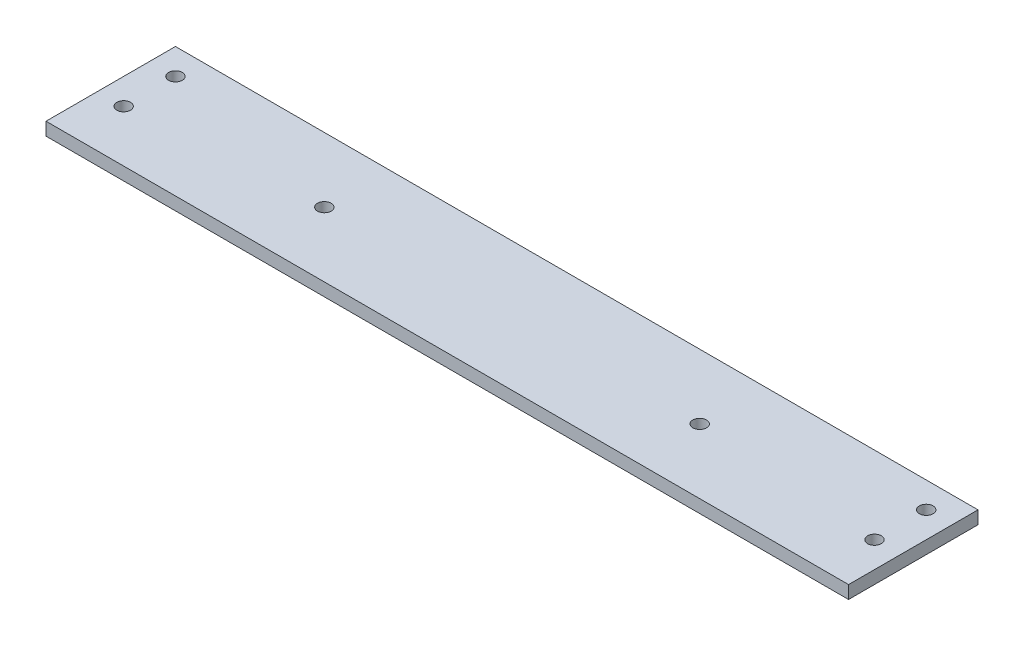
SolidWorks part; units mm, degrees
ref_plane "Front Plane" through (0, 0, 0) normal (0, 0, 1) x (1, 0, 0)
ref_plane "Top Plane" through (0, 0, 0) normal (0, 1, 0) x (1, 0, 0)
ref_plane "Right Plane" through (0, 0, 0) normal (1, 0, 0) x (0, 0, -1)
sketch "Sketch1" plane through (0, 0, 0) normal (0, 1, 0) x (1, 0, 0)
  line L1 (-196.85, -31.75) -> (196.85, -31.75)
  line L2 (-196.85, -31.75) -> (-196.85, 31.75)
  line L3 (-196.85, 31.75) -> (196.85, 31.75)
  line L4 (196.85, -31.75) -> (196.85, 31.75)
  line L5 (-196.85, -31.75) -> (196.85, 31.75) construction
  line L6 (-196.85, 31.75) -> (196.85, -31.75) construction
  point P0 (0, 0)
  dimension "D1" = 63.5
  dimension "D2" = 393.7
extrude "Boss-Extrude1" add sketch "Sketch1" along normal blind 6.35
sketch "Sketch2" plane through (0, 0, 0) normal (0, -1, 0) x (1, 0, 0)
  line L0 (196.85, -31.75) -> (-196.85, -31.75) construction
  line L1 (-196.85, -31.75) -> (-196.85, 31.75) construction
  line L2 (196.85, 31.75) -> (196.85, -31.75) construction
  circle A0 centre (-184.15, -19.05) radius 3.3655
  circle A1 centre (-184.15, 6.35) radius 3.3655
  circle A2 centre (184.15, -19.05) radius 3.3655
  circle A3 centre (184.15, 6.35) radius 3.3655
  circle A4 centre (92.075, 0) radius 2.5527 construction
  circle A5 centre (-92.0623, 0) radius 2.5527 construction
  circle A6 centre (92.075, 0) radius 2.5527
  circle A7 centre (-92.0623, 0) radius 2.5527
  circle A8 centre (-92.0623, 0) radius 3.3655
  circle A9 centre (92.075, 0) radius 3.3655
  dimension "D1" = 6.731
  dimension "D2" = 6.731
  dimension "D6" = 6.731
  dimension "D8" = 6.731
  dimension "D12" = 6.731
  dimension "D13" = 6.731
  dimension "D3" = 12.7
  dimension "D4" = 25.4
  dimension "D5" = 12.7
  dimension "D7" = 12.7
  dimension "D9" = 12.7
  dimension "D10" = 12.7
  dimension "D11" = 25.4
extrude "Cut-Extrude1" cut sketch "Sketch2" against normal through all contours A7 | A8 A7 | A1 | A0 | A9 A6 | A6 | A3 | A2
